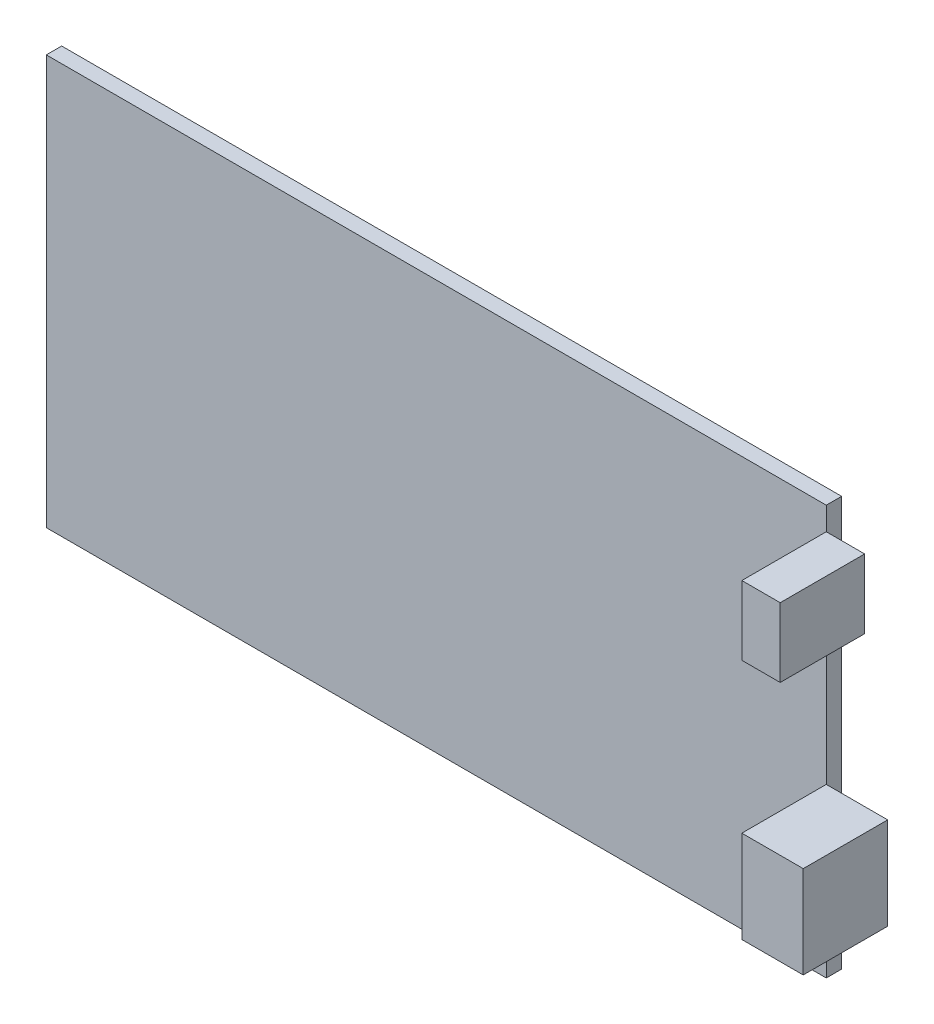
SolidWorks part; units mm, degrees
ref_plane "Plano frontal" through (0, 0, 0) normal (0, 0, 1) x (1, 0, 0)
ref_plane "Plano superior" through (0, 0, 0) normal (0, 1, 0) x (1, 0, 0)
ref_plane "Plano direito" through (0, 0, 0) normal (1, 0, 0) x (0, 0, -1)
sketch "Esboço1" plane through (0, 0, 0) normal (0, 0, 1) x (1, 0, 0)
  line L1 (0, 0) -> (101.6, 0)
  line L2 (0, 0) -> (0, 53.34)
  line L3 (0, 53.34) -> (101.6, 53.34)
  line L4 (101.6, 0) -> (101.6, 53.34)
  dimension "D1" = 101.6
  dimension "D2" = 53.34
extrude "Ressalto-extrusão1" add sketch "Esboço1" along normal blind 2
sketch "Esboço2" plane through (101.6, 0, 0) normal (1, 0, 0) x (0, 0, -1)
  line L0 (-2, 0) -> (-2, 53.34) construction
  line L1 (-2, 50.34) -> (-13, 50.34)
  line L2 (-2, 50.34) -> (-2, 41.34)
  line L3 (-2, 41.34) -> (-13, 41.34)
  line L4 (-13, 50.34) -> (-13, 41.34)
  line L5 (-2, 53.34) -> (0, 53.34) construction
  line L7 (-2, 21.84) -> (-13, 21.84)
  line L8 (-2, 21.84) -> (-2, 9.84)
  line L9 (-2, 9.84) -> (-13, 9.84)
  line L10 (-13, 21.84) -> (-13, 9.84)
  dimension "D1" = 11
  dimension "D2" = 9
  dimension "D3" = 3
  dimension "D4" = 40.5
  dimension "D5" = 11
  dimension "D6" = 12
extrude "Ressalto-extrusão2" add sketch "Esboço2" along normal blind 5 separate body
sketch "Esboço3" plane through (106.6, 0, 0) normal (1, 0, 0) x (0, 0, -1)
  line L4 (-2, 9.84) -> (-2, 21.84)
  line L5 (-2, 21.84) -> (-13, 21.84)
  line L6 (-13, 21.84) -> (-13, 9.84)
  line L7 (-13, 9.84) -> (-2, 9.84)
  line L8 (-2, 9.84) -> (-2, 21.84)
  line L9 (-2, 21.84) -> (-13, 21.84)
  line L10 (-13, 21.84) -> (-13, 9.84)
  line L11 (-13, 9.84) -> (-2, 9.84)
  dimension "D1" = 0
extrude "Ressalto-extrusão3" add sketch "Esboço3" along normal blind 3
